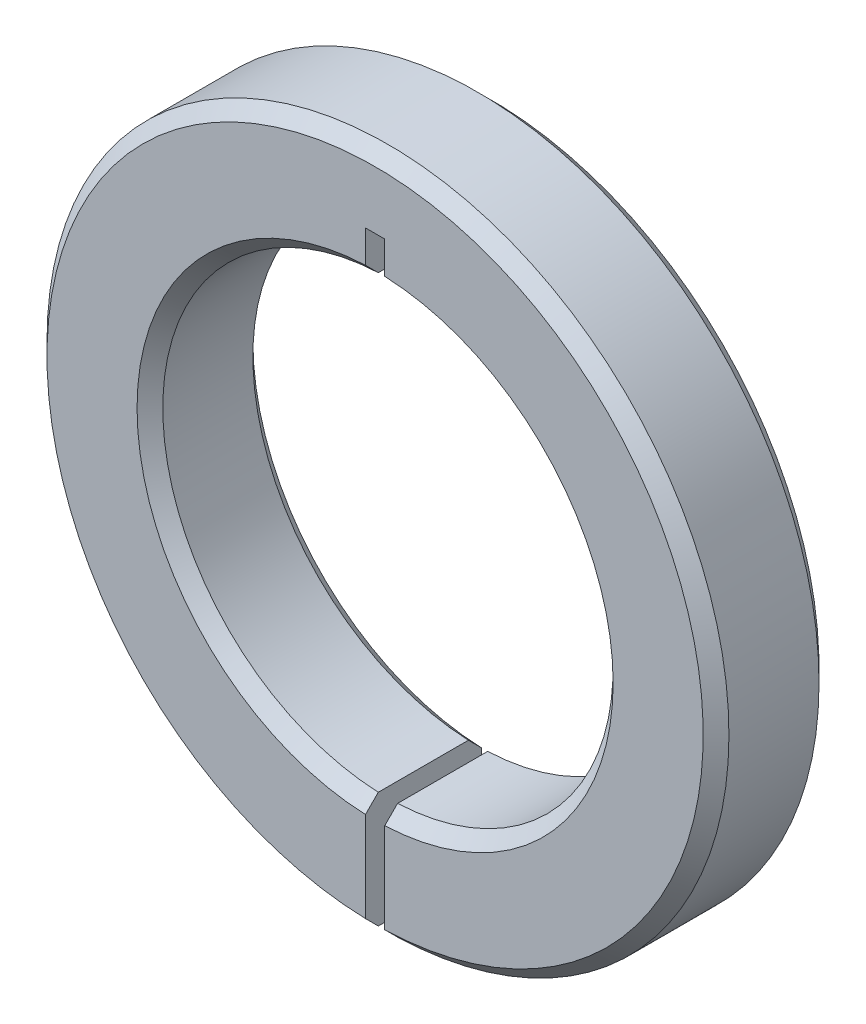
SolidWorks part; units mm, degrees
material "Alloy Steel"
ref_plane "Front Plane" through (0, 0, 0) normal (0, 0, 1) x (1, 0, 0)
ref_plane "Top Plane" through (0, 0, 0) normal (0, 1, 0) x (1, 0, 0)
ref_plane "Right Plane" through (0, 0, 0) normal (1, 0, 0) x (0, 0, -1)
sketch "Sketch1" plane through (0, 0, 0) normal (0, 0, 1) x (1, 0, 0)
  line L0 (-0.75, 21) -> (0.75, 21)
  line L1 (0.75, 21) -> (0.75, 17.4839)
  line L2 (-0.75, 21) -> (-0.75, 17.4839)
  line L3 (0.75, -17.4839) -> (0.75, -26.4894)
  line L4 (-0.75, -17.4839) -> (-0.75, -26.4894)
  arc A0 (0.75, -17.4839) -> (0.75, 17.4839) centre (0, 0) ccw
  arc A1 (0.75, -26.4894) -> (-0.75, -26.4894) centre (0, 0) ccw
  arc A2 (-0.75, 17.4839) -> (-0.75, -17.4839) centre (0, 0) ccw
  point P1 (0, 0)
  point P7 (0, 21)
  dimension "D1" = 35
  dimension "D2" = 9
  dimension "D3" = 21
  dimension "D4" = 1.5
extrude "Boss-Extrude1" add sketch "Sketch1" along normal blind 9
chamfer "Chamfer1" distance 1 angle 45 6 edges at (-17.5, 0, 0) (17.5, 0, 0) (-17.5, 0, 9) (17.5, 0, 9) (0, 26.5, 0) (0, 26.5, 9)
sketch "Sketch2" plane through (0, 0, 0) normal (1, 0, 0) x (0, 0, -1)
  line L0 (0, -25.489) -> (0, 25.5) construction
  circle A0 centre (-4.5, -22) radius 2
  dimension "D1" = 4
  dimension "D2" = 22
  dimension "D3" = 4.5
extrude "Cut-Extrude1" cut sketch "Sketch2" against normal mid plane 14
ref_plane "Plane1" through (7, 0, 0) normal (1, 0, 0) x (0, 0, -1)
sketch "Sketch3" plane through (7, 0, 0) normal (1, 0, 0) x (0, 0, -1)
  line L0 (0, -25.489) -> (0, 25.5) construction
  circle A0 centre (-4.5, -22) radius 3
  dimension "D1" = 6
  dimension "D2" = 22
  dimension "D3" = 4.5
extrude "Cut-Extrude2" cut sketch "Sketch3" along normal through all
mirror "Mirror1" about plane through (0, 0, 0) normal (1, 0, 0) of "Cut-Extrude2"
